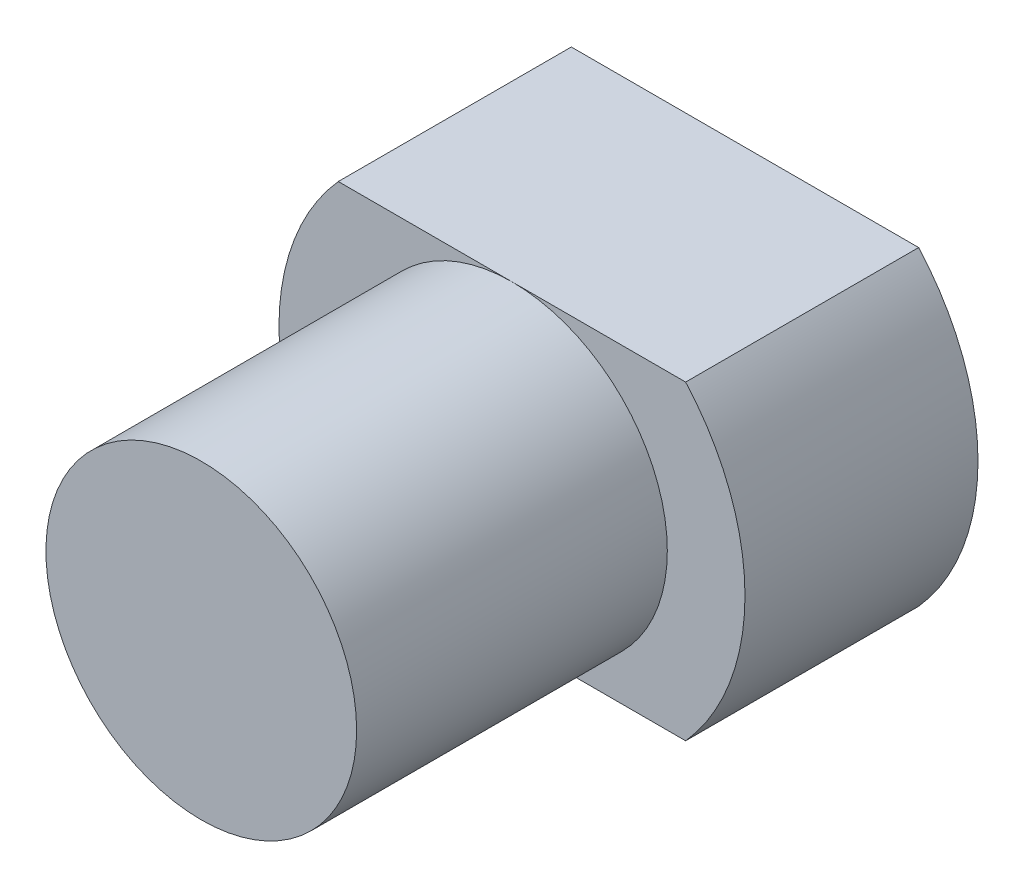
SolidWorks part; units mm, degrees
ref_plane "Front Plane" through (0, 0, 0) normal (0, 0, 1) x (1, 0, 0)
ref_plane "Top Plane" through (0, 0, 0) normal (0, 1, 0) x (1, 0, 0)
ref_plane "Right Plane" through (0, 0, 0) normal (1, 0, 0) x (0, 0, -1)
sketch "Sketch2" plane through (0, 0, 0) normal (0, 0, 1) x (1, 0, 0)
  line L0 (0, 0) -> (50000, 0) construction
  line L1 (-14.199, 12.7) -> (14.199, 12.7)
  line L2 (-14.199, -12.7) -> (14.199, -12.7)
  arc A0 (14.199, -12.7) -> (14.199, 12.7) centre (0, 0) ccw
  arc A1 (-14.199, 12.7) -> (-14.199, -12.7) centre (0, 0) ccw
  dimension "D1" = 38.1
  dimension "D2" = 25.4
extrude "Boss-Extrude1" add sketch "Sketch2" along normal blind 19.05
sketch "Sketch3" plane through (0, 0, 19.05) normal (0, 0, 1) x (1, 0, 0)
  line L0 (14.199, 12.7) -> (-14.199, 12.7) construction
  circle A0 centre (0, 0) radius 12.7
extrude "Boss-Extrude2" add sketch "Sketch3" along normal blind 25.4
